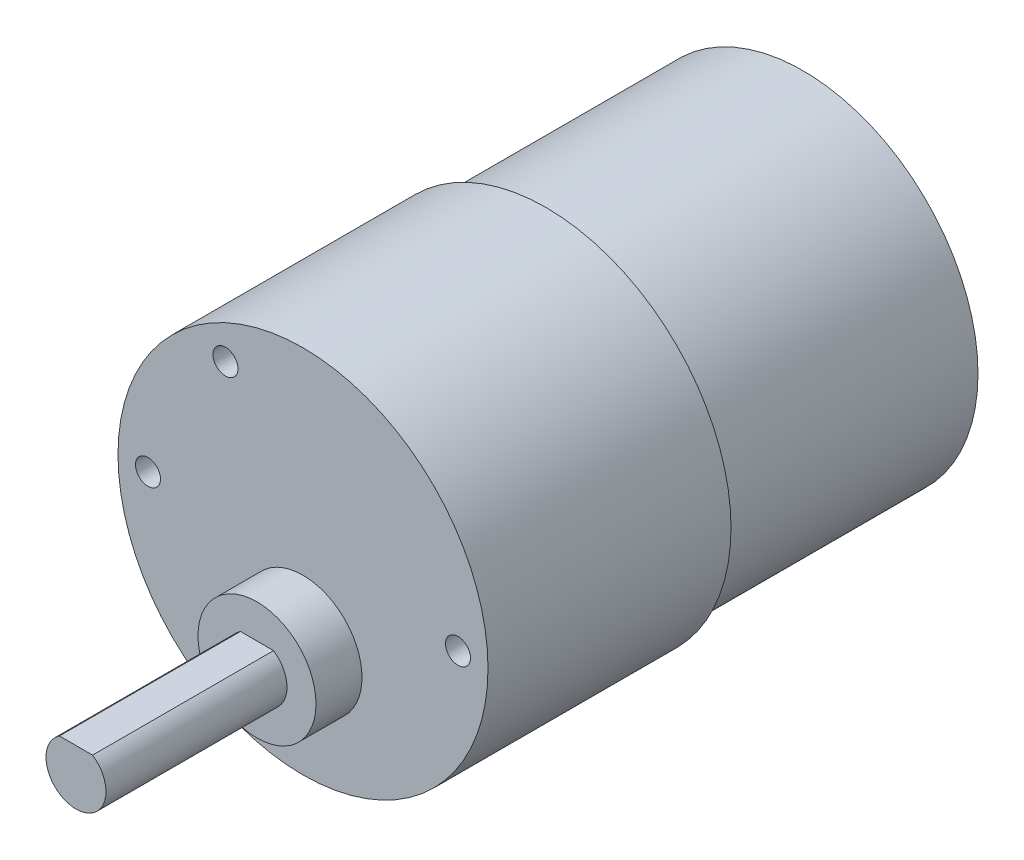
SolidWorks part; units mm, degrees
material "Plain Carbon Steel"
ref_plane "Front Plane" through (0, 0, 0) normal (0, 0, 1) x (1, 0, 0)
ref_plane "Top Plane" through (0, 0, 0) normal (0, 1, 0) x (1, 0, 0)
ref_plane "Right Plane" through (0, 0, 0) normal (1, 0, 0) x (0, 0, -1)
sketch "Sketch3" plane through (0, 0, 0) normal (0, 0, 1) x (1, 0, 0)
  line L2 (226.6601, 676.4611) -> (1226.6601, 676.4611) construction
  line L3 (-1.6583, -4.6) -> (1.6583, -4.6)
  circle A1 centre (0, 0) radius 18.5
  circle A5 centre (0, -7.1) radius 5.9
  arc A6 (-1.6583, -4.6) -> (1.6583, -4.6) centre (0, -7.1) ccw
  arc A7 (1.6583, -4.6) -> (-1.6583, -4.6) centre (0, -7.1) ccw construction
  circle A8 centre (0, 0) radius 15.5 construction
  dimension "D1" = 11.8
  dimension "D2" = 37
  dimension "D3" = 7.1
  dimension "D4" = 6
  dimension "D6" = 31
  dimension "D5" = 5.5
sketch "Sketch4" plane through (0, 0, 0) normal (1, 0, 0) x (0, 0, -1)
  line L0 (0, 0) -> (4.4998, 0) construction
  line L7 (0, 0) -> (0, 18.5)
  line L8 (0, 18.5) -> (24.3, 18.5)
  line L9 (24.3, 18.5) -> (50, 18.5) construction
  line L10 (50, 17.5) -> (50, 0)
  line L16 (50, 0) -> (0, 0)
  line L17 (24.3, 18.5) -> (24.3, 17.5)
  line L18 (24.3, 17.5) -> (50, 17.5)
  line L19 (50, 18.5) -> (50, 17.5) construction
  point P2 (24.3, 17.3616)
  point P10 (24.3, 17.788)
  dimension "D1" = 1
  dimension "D3" = 24.3
  dimension "D4" = 25.7
revolve "Revolve1" add sketch "Sketch4" angle 360 about L0
sketch "Sketch12" plane through (0, 0, 0) normal (0, 0, 1) x (1, 0, 0)
  line L0 (-1.6583, -4.6) -> (1.6583, -4.6) construction
  line L1 (-1.6583, -4.6) -> (1.6583, -4.6)
  arc A0 (-1.6583, -4.6) -> (1.6583, -4.6) centre (0, -7.1) ccw construction
  arc A1 (-1.6583, -4.6) -> (1.6583, -4.6) centre (0, -7.1) ccw
extrude "Boss-Extrude1" add sketch "Sketch12" along normal offset from surface (22.7 mm away) 72.7 up to face at (17.5, 0, -50)
sketch "Sketch13" plane through (0, 0, 0) normal (0, 0, 1) x (1, 0, 0)
  circle A0 centre (0, -7.1) radius 5.9 construction
  circle A1 centre (0, -7.1) radius 5.9
extrude "Boss-Extrude2" add sketch "Sketch13" along normal offset from surface (4.6 mm away) 18.1 up to face at (0, -7.35, 22.7)
hole_wizard "Tap Drill for M3x0.5 Tap1" positions "Sketch7" profile "Sketch8" hole size "M3x0.5" standard "ANSI Metric"
sketch "Sketch7" plane through (0, 0, 0) normal (0, 0, 1) x (1, 0, 0)
  circle A1 centre (0, 0) radius 15.5 construction
  circle A2 centre (0, 0) radius 15.5 construction
  point P17 (-15.5, 0)
  point P19 (-7.75, 13.4234)
  point P21 (-7.75, -13.4234)
  point P25 (15.5, 0)
  dimension "D1" = 15.5
sketch "Sketch8" plane through (15.5, 0, 0) normal (1, 0, 0) x (0, -1, 0)
  line L0 (0, 0) -> (0, 3.7511)
  line L1 (0, 3.7511) -> (1.25, 3)
  line L2 (1.25, 3) -> (1.25, 0)
  line L5 (1.25, 0) -> (0, 0)
  line L10 (0, 3.7511) -> (-1.25, 3) construction
  line L11 (0, -6.35) -> (0, 107.95) construction
  dimension "Hole Dia." = 2.5
  dimension "Hole Depth" = 3
  dimension "Drill Angle" = 118
